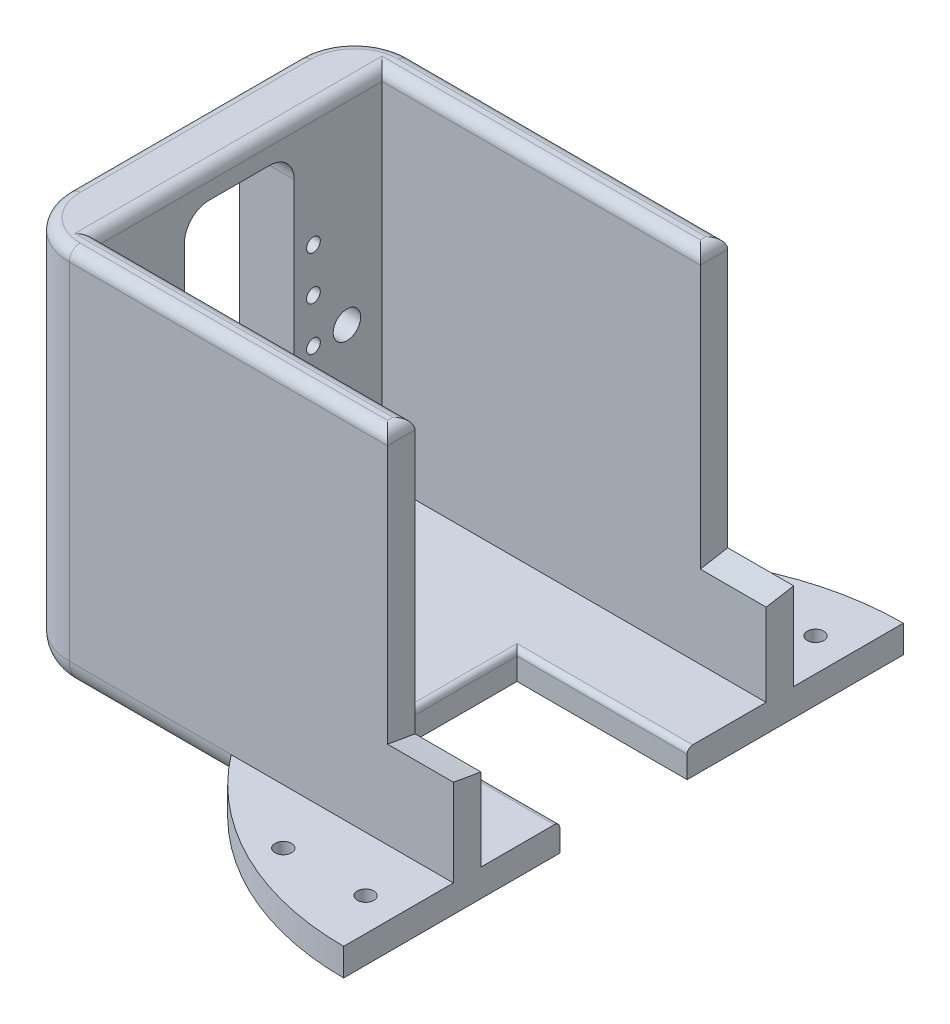
SolidWorks part; units mm, degrees
ref_plane "Plan de face" through (0, 0, 0) normal (0, 0, 1) x (1, 0, 0)
ref_plane "Plan de dessus" through (0, 0, 0) normal (0, 1, 0) x (1, 0, 0)
ref_plane "Plan de droite" through (0, 0, 0) normal (1, 0, 0) x (0, 0, -1)
sketch "Esquisse1" plane through (0, 0, 0) normal (0, 1, 0) x (1, 0, 0)
  line L0 (-50.0182, 0) -> (81.7007, 0) construction
  line L1 (-40.4969, 31) -> (0, 31)
  line L2 (-70, 26) -> (-40.4969, 26)
  line L3 (-70, 26) -> (-70, -26)
  line L4 (0, 31) -> (0, -31)
  line L5 (0, 68.3448) -> (0, -68.3448) construction
  line L6 (-40.4969, 31) -> (-80, 31)
  line L7 (-80, 31) -> (-80, -31)
  line L8 (-80, -31) -> (-40.4969, -31)
  line L9 (-70, -26) -> (-40.4969, -26)
  line L10 (-40.4969, 26) -> (0, 26)
  line L11 (-40.4969, -26) -> (0, -26)
  line L12 (-40.4969, -31) -> (0, -31)
  point P14 (-50, 0)
  dimension "D1" = 80
  dimension "D2" = 62
  dimension "D4" = 10
  dimension "D5" = 5
extrude "Boss.-Extru.5" add sketch "Esquisse1" along normal mid plane 100
sketch "Esquisse5" plane through (-70, 0, 0) normal (1, 0, 0) x (0, 0, -1)
  line L1 (-10, -2) -> (10, -2)
  line L2 (-10, -2) -> (-10, -33.8)
  line L3 (-10, -33.8) -> (10, -33.8)
  line L4 (10, -2) -> (10, -33.8)
  line L5 (-10, -2) -> (-10, 5.5)
  line L6 (10, -2) -> (10, 5.5)
  line L7 (-5.5, 10) -> (5.5, 10)
  arc A0 (-10, 5.5) -> (-5.5, 10) centre (-5.5, 5.5) cw
  arc A1 (5.5, 10) -> (10, 5.5) centre (5.5, 5.5) cw
  circle A2 centre (0, 0) radius 2.15
  dimension "D3" = 4.3
  dimension "D6" = 4.5
  dimension "D7" = 4.5
  dimension "D1" = 2
  dimension "D2" = 10
  dimension "D4" = 43.8
  dimension "D5" = 20
  dimension "D8" = 12
extrude "Enlèv. mat.-Extru.1" cut sketch "Esquisse5" against normal blind 10 contours A2 L1 L6 A1 L7 A0 L5 | A2 L1 L2 L3 L4 | L1 A2 | L1 A2
sketch "Esquisse8" plane through (0, -50, 0) normal (0, 1, 0) x (1, 0, 0)
  line L0 (0, -51) -> (0, 51)
  line L1 (-40.5, -31) -> (-80, -31)
  line L2 (-80, -31) -> (-80, 31)
  line L3 (-80, 31) -> (-40.5, 31)
  line L4 (0, -26) -> (0, -31) construction
  line L5 (-80, -31) -> (0, -31) construction
  line L6 (-80, 0) -> (-0.0031, 0) construction
  arc A1 (0, -51) -> (-40.5, -31) centre (-0.0031, 0) cw
  arc A3 (-40.5, 31) -> (0, 51) centre (-0.0031, 0) cw
  dimension "D1" = 51
  dimension "D2" = 51
  dimension "D3" = 40.5
  dimension "D4" = 20
extrude "Boss.-Extru.6" add sketch "Esquisse8" against normal blind 5
sketch "Esquisse9" plane through (0, 0, 0) normal (1, 0, 0) x (0, 0, -1)
  line L1 (31, 50) -> (31, -50) construction
  line L2 (-31, 50) -> (31, 50)
  line L3 (-31, 50) -> (-31, 15)
  line L4 (-31, 15) -> (31, 15)
  line L8 (0, -5.2261) -> (0, 54.1477) construction
  line L9 (31, 50) -> (31, 15)
  line L10 (-5.5, 10) -> (5.5, 10) construction
  dimension "D1" = 5
sketch "Esquisse11" plane through (-70, 0, 0) normal (1, 0, 0) x (0, 0, -1)
  line L0 (0, 0) -> (0, -23.2285) construction
  line L3 (26, -50) -> (-26, -50) construction
  circle A0 centre (-19.6, -22.214) radius 2.5
  circle A1 centre (19.6, -22.214) radius 2.5
  circle A2 centre (0, 126.5) radius 150
  point P6 (0, -23.5)
  dimension "D1" = 300
  dimension "D3" = 5
  dimension "D2" = 23.5
  dimension "D4" = 39.2
  dimension "D6" = 27.786
extrude "Enlèv. mat.-Extru.9" cut sketch "Esquisse11" against normal blind 5 contours A0 | A1
fillet "Congé1" radius 10 2 edges at (-80, -2.5, 31) (-80, -2.5, -31)
sketch "Esquisse10" plane through (0, 0, 0) normal (1, 0, 0) x (0, 0, -1)
  line L0 (85.2632, 65.694) -> (136.2871, 33.4867)
  line L1 (0, 23.2055) -> (0, -37) construction
  line L2 (-136.2871, 33.4867) -> (-85.2632, 65.694)
  line L3 (85.2632, 65.694) -> (136.2871, 33.4867) construction
  arc A0 (-85.2632, 65.694) -> (85.2632, 65.694) centre (0, 130) ccw
  arc A1 (-136.2871, 33.4867) -> (136.2871, 33.4867) centre (0, 130) ccw
  arc A3 (-73.5134, 52.5348) -> (49.5522, 35.3974) centre (0, 130) ccw
  point P0 (0, 23.2055)
  dimension "D3" = 37
  dimension "D7" = 167
  dimension "D10" = 11.7498
extrude "Enlèv. mat.-Extru.12" cut sketch "Esquisse10" against normal blind 12
sketch "Esquisse12" plane through (0, -55, 0) normal (0, -1, 0) x (-1, 0, 0)
  line L0 (5.4841, 0) -> (-5.4841, 0) construction
  line L8 (31, -11.6) -> (0, -11.6)
  line L9 (31, -11.6) -> (31, 11.6)
  line L10 (31, 11.6) -> (0, 11.6)
  line L11 (0, -11.6) -> (0, 11.6)
  line L12 (0, -51) -> (0, 51) construction
  dimension "D2" = 23.2
  dimension "D10" = 31
extrude "Enlèv. mat.-Extru.13" cut sketch "Esquisse12" against normal blind 10
fillet "Congé2" radius 1 3 edges at (-15.5, -50, -11.6) (-31, -50, 0) (-15.5, -50, 11.6)
extrude "Enlèv. mat.-Extru.14" cut sketch "Esquisse9" against normal through all
fillet "Congé3" radius 5 5 edges at (-55.25, -55, 31) (-77.0711, -55, 28.0711) (-80, -55, 0) (-77.0711, -55, -28.0711) (-55.25, -55, -31)
fillet "Congé4" radius 2 9 edges at (-12, 15, -28.5) (-41, 15, -26) (-41, 15, -31) (-77.0711, 15, -28.0711) (-80, 15, 0) (-77.0711, 15, 28.0711) (-70, 15, 0) (-41, 15, 26) (-41, 15, 31)
sketch "Esquisse13" plane through (0, -50, 0) normal (0, 1, 0) x (1, 0, 0)
  line L0 (0, 41) -> (-30.3346, 41) construction
  line L1 (0, 31) -> (0, 51) construction
  line L2 (0, 0) -> (-93.9493, 0) construction
  line L3 (0, -41) -> (-30.3346, -41) construction
  arc A0 (0, 51) -> (-40.5, 31) centre (-0.0031, 0) ccw construction
  circle A1 centre (-21, 41) radius 1.5
  circle A2 centre (-6, 41) radius 1.5
  circle A3 centre (-6, -41) radius 1.5
  circle A4 centre (-21, -41) radius 1.5
  dimension "D1" = 3
  dimension "D2" = 15
  dimension "D3" = 6
extrude "Enlèv. mat.-Extru.15" cut sketch "Esquisse13" against normal through all
sketch "Esquisse14" plane through (-70, 0, 0) normal (1, 0, 0) x (0, 0, -1)
  line L1 (0, 0) -> (0, -33.0017) construction
  circle A0 centre (-13.5, -6.5) radius 1.25
  circle A1 centre (-13.5, -14.5) radius 1.25
  circle A2 centre (-13.5, -22.5) radius 1.25
  circle A3 centre (-13.5, -30.5) radius 1.25
  circle A4 centre (13.5, -30.5) radius 1.25
  circle A5 centre (13.5, -22.5) radius 1.25
  circle A6 centre (13.5, -14.5) radius 1.25
  circle A7 centre (13.5, -6.5) radius 1.25
  dimension "D1" = 2.5
  dimension "D2" = 8
  dimension "D3" = 13.5
  dimension "D4" = 8
  dimension "D5" = 8
  dimension "D6" = 6.5
hole_wizard "Trou taraudé M31" positions "Esquisse3D1" profile "Esquisse15" tap size "M3" standard "Iso"
sketch3d "Esquisse3D1"
  point P0 (-70, -6.5, 13.5)
  point P3 (-70, -6.5, -13.5)
  point P6 (-70, -14.5, -13.5)
  point P9 (-70, -14.5, 13.5)
  point P12 (-70, -22.5, 13.5)
  point P15 (-70, -22.5, -13.5)
  point P17 (-70, -30.5, -13.5)
  point P19 (-70, -30.5, 13.5)
sketch "Esquisse15" plane through (-70, -6.5, 13.5) normal (0, 1, 0) x (0, 0, -1)
  line L0 (0, 0) -> (0, 13.2511)
  line L1 (0, 13.2511) -> (1.25, 12.5)
  line L2 (1.25, 12.5) -> (1.25, 0)
  line L5 (1.25, 0) -> (0, 0)
  line L10 (0, 13.2511) -> (-1.25, 12.5) construction
  line L11 (0, -6.35) -> (0, 107.95) construction
  dimension "Diamètre du trou pour taraudage" = 2.5
  dimension "Profondeur du trou pour taraudage" = 12.5
  dimension "Angle de pointe" = 118
cosmetic thread "Filetage de perçage1" parameters "D1"=10, "D2"=3
cosmetic thread "Filetage de perçage2" parameters "D1"=10, "D2"=3
cosmetic thread "Filetage de perçage3" parameters "D1"=10, "D2"=3
cosmetic thread "Filetage de perçage4" parameters "D1"=10, "D2"=3
cosmetic thread "Filetage de perçage5" parameters "D1"=10, "D2"=3
cosmetic thread "Filetage de perçage6" parameters "D1"=10, "D2"=3
cosmetic thread "Filetage de perçage7" parameters "D1"=10, "D2"=3
cosmetic thread "Filetage de perçage8" parameters "D1"=10, "D2"=3
sketch3d "Esquisse3D2"
  circle A0 centre (-80, -6.5, 13.5) radius 1.75
  circle A1 centre (-80, -14.5, 13.5) radius 1.75
  circle A2 centre (-80, -22.5, 13.5) radius 1.75
  circle A3 centre (-80, -6.5, -13.5) radius 1.75
  circle A4 centre (-80, -14.5, -13.5) radius 1.75
  circle A5 centre (-80, -22.5, -13.5) radius 1.75
  circle A6 centre (-80, -30.5, -13.5) radius 1.75
  circle A7 centre (-80, -30.5, 13.5) radius 1.75
  point P2 (-78.25, -6.5, 13.5)
  point P6 (-78.25, -14.5, 13.5)
  point P10 (-78.25, -22.5, 13.5)
  point P14 (-78.25, -6.5, -13.5)
  point P18 (-78.25, -14.5, -13.5)
  point P22 (-78.25, -22.5, -13.5)
  point P26 (-78.25, -30.5, -13.5)
  point P30 (-78.25, -30.5, 13.5)
  dimension "D1" = 3.5
  dimension "D2" = 3.5
  dimension "D3" = 3.5
  dimension "D4" = 3.5
  dimension "D5" = 3.5
  dimension "D6" = 3.5
  dimension "D7" = 3.5
  dimension "D8" = 3.5
extrude "Enlèv. mat.-Extru.16" cut sketch "Esquisse3D2" along direction (1, 0, 0) on the side against the normal blind 8
sketch3d "Esquisse3D3"
  line L1 (-80, -44, 6) -> (-80, -44, -6)
  line L2 (-80, -44, 6) -> (-80, -50, 6)
  line L3 (-80, -50, 6) -> (-80, -50, -6)
  line L4 (-80, -44, -6) -> (-80, -50, -6)
  line L6 (-80, -50, -21) -> (-80, -50, 21) construction
  point P4 (-80, -50, -21)
  dimension "D1" = 6
  dimension "D2" = 12
  dimension "D3" = 6
extrude "Enlèv. mat.-Extru.17" cut sketch "Esquisse3D3" along direction (1, 0, 0) on the side of the normal up to next (10 mm away)
